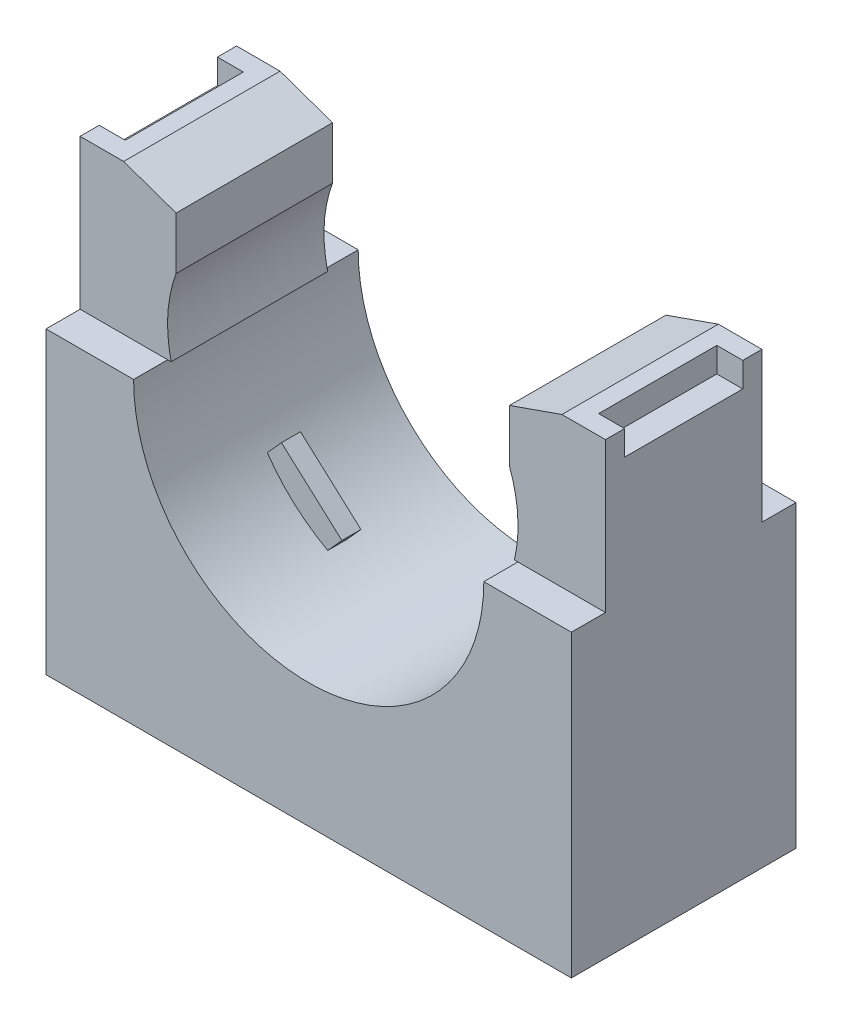
SolidWorks part; units mm, degrees
ref_plane "Front Plane" through (0, 0, 0) normal (0, 0, 1) x (1, 0, 0)
ref_plane "Top Plane" through (0, 0, 0) normal (0, 1, 0) x (1, 0, 0)
ref_plane "Right Plane" through (0, 0, 0) normal (1, 0, 0) x (0, 0, -1)
sketch "Sketch1" plane through (0, 0, 0) normal (0, 0, 1) x (1, 0, 0)
  line L0 (-17.526, -14.986) -> (17.526, 14.986) construction
  line L1 (-17.526, 14.986) -> (17.526, 14.986)
  line L2 (-17.526, 14.986) -> (-17.526, -14.986)
  line L3 (-17.526, -14.986) -> (17.526, -14.986)
  line L4 (17.526, 14.986) -> (17.526, -14.986)
  arc A0 (-11.4485, 2.6611) -> (11.4525, 2.6811) centre (0, 4.9953) ccw construction
  point P4 (0, 0)
  dimension "D3" = 19.9813
  dimension "D4" = 11.684
  dimension "B" = 35.052
  dimension "C" = 29.972
extrude "Extrude1" add sketch "Sketch1" along normal blind 14.986
sketch "Sketch2" plane through (0, 0, 14.986) normal (0, 0, 1) x (1, 0, 0)
  line L1 (-11.684, 4.9953) -> (-11.4503, 4.9953)
  line L2 (11.4503, 4.9953) -> (11.684, 4.9953)
  line L3 (11.1204, 10.2579) -> (11.1204, 13.7583)
  line L4 (11.1204, 13.7583) -> (14.6209, 14.986)
  line L5 (17.526, 14.986) -> (-17.526, 14.986) construction
  line L6 (0, 0) -> (0, 22.8281) construction
  line L7 (-11.1204, 13.7583) -> (-14.6209, 14.986)
  line L8 (-11.1204, 10.2579) -> (-11.1204, 13.7583)
  line L9 (14.6209, 14.986) -> (-14.6209, 14.986)
  line L10 (17.526, -14.986) -> (17.526, 14.986) construction
  arc A0 (-11.684, 4.9953) -> (11.684, 4.9953) centre (0, 4.9953) ccw
  arc A1 (11.1204, 10.2579) -> (11.4503, 4.9953) centre (2.5551, 7.0794) cw
  arc A2 (-11.1204, 10.2579) -> (-11.4503, 4.9953) centre (-2.5551, 7.0794) ccw
  arc A3 (-11.4485, 2.6611) -> (11.4525, 2.6811) centre (0, 4.9953) ccw construction
  dimension "D1" = 0.2337
  dimension "D3" = 9.1361
  dimension "D2" = 3.5004
  dimension "D4" = 3.5004
  dimension "D7" = 6.4056
  dimension "D8" = 5.2626
extrude "Cut-Extrude1" cut sketch "Sketch2" against normal through all
sketch "Sketch3" plane through (0, 0, 0) normal (1, 0, 0) x (0, 0, -1)
  line L1 (-14.986, 4.9953) -> (-12.7114, 4.9953)
  line L2 (-12.7114, 14.986) -> (-12.7114, 4.9953)
  line L3 (-14.986, 4.9953) -> (-14.986, 14.986)
  line L4 (-2.2746, 14.986) -> (-2.2746, 4.9953)
  line L5 (-7.493, 31.6865) -> (-7.493, 10.4775) construction
  line L6 (-14.986, 14.986) -> (0, 14.986) construction
  line L7 (-14.986, -14.986) -> (-14.986, 14.986) construction
  line L8 (-14.986, 14.986) -> (-12.7114, 14.986)
  line L9 (0, 4.9953) -> (0, 14.986)
  line L10 (0, 4.9953) -> (-2.2746, 4.9953)
  line L11 (-2.2746, 14.986) -> (0, 14.986)
  line L13 (0, -14.986) -> (0, 14.986) construction
  dimension "D2" = 2.2746
extrude "Cut-Extrude2" cut sketch "Sketch3" against normal through all and the other way through all
sketch "Sketch4" plane through (0, -14.986, 0) normal (0, -1, 0) x (1, 0, 0)
  line L12 (-17.526, 14.1922) -> (17.526, 14.1922)
  line L13 (-16.7322, 14.1922) -> (16.7323, 14.1922)
  line L14 (-16.7322, 0.7937) -> (-16.7322, 14.986)
  line L15 (16.7323, 0.7937) -> (-16.7322, 0.7937)
  line L16 (16.7323, 14.986) -> (16.7323, 0.7937)
  line L17 (-16.7322, 0.7937) -> (-16.7322, 14.1922)
  line L18 (16.7323, 0.7937) -> (-16.7322, 0.7937)
  line L19 (16.7323, 14.1922) -> (16.7323, 0.7937)
  dimension "D1" = 0.7937
  dimension "D2" = 0.7937
extrude "Cut-Extrude3" cut sketch "Sketch4" against normal blind 0.254
sketch "Sketch5" plane through (0, 14.986, 0) normal (0, 1, 0) x (1, 0, 0)
  line L0 (-17.526, -2.2746) -> (-14.6209, -2.2746) construction
  line L2 (-17.526, -3.5503) -> (-15.7946, -3.5503)
  line L3 (-17.526, -3.5503) -> (-17.526, -11.4357)
  line L4 (-17.526, -11.4357) -> (-15.7946, -11.4357)
  line L6 (-15.7946, -3.5503) -> (-15.7946, -11.4357)
  line L10 (17.526, -3.5503) -> (15.7946, -3.5503)
  line L11 (17.526, -3.5503) -> (17.526, -11.4357)
  line L12 (17.526, -11.4357) -> (15.7946, -11.4357)
  line L13 (15.7946, -3.5503) -> (15.7946, -11.4357)
  line L14 (17.526, -12.7114) -> (17.526, -2.2746) construction
  line L15 (-17.526, -12.7114) -> (-17.526, -2.2746) construction
  line L16 (14.6209, -7.493) -> (-14.6209, -7.493) construction
  line L17 (14.6209, -2.2746) -> (14.6209, -12.7114) construction
  line L18 (-14.6209, -2.2746) -> (-14.6209, -12.7114) construction
  dimension "D1" = 1.2757
  dimension "D2" = 1.1737
extrude "Cut-Extrude4" cut sketch "Sketch5" against normal blind 1.651
ref_plane "Plane1" through (0, 0, 7.493) normal (0, 0, -1) x (-1, 0, 0)
sketch "Sketch6" plane through (0, 0, 7.493) normal (0, 0, -1) x (-1, 0, 0)
  line L0 (0, 0) -> (0, -34.0604) construction
  line L1 (3.048, -14.732) -> (0, -14.732)
  line L2 (16.7322, -14.732) -> (-16.7323, -14.732) construction
  line L3 (0, -8.636) -> (5.969, -8.636)
  line L4 (5.969, -8.636) -> (5.969, -11.684)
  line L5 (5.969, -11.684) -> (3.048, -11.684)
  line L6 (3.048, -11.684) -> (3.048, -14.732)
  line L7 (0, -14.732) -> (0, -8.636)
  dimension "E" = 11.938
  dimension "D" = 6.096
  dimension "D3" = 3.048
  dimension "D4" = 6.096
revolve "Cut-Revolve1" cut sketch "Sketch6" angle 360 about L0
sketch "Sketch7" plane through (0, 0, 7.493) normal (0, 0, -1) x (-1, 0, 0)
  line L0 (0, 16.5622) -> (0, -24.4387) construction
  line L1 (0, 4.9953) -> (6.6588, -2.4) construction
  line L2 (4.6414, -4.2164) -> (8.6761, -0.5836)
  line L3 (8.6761, -0.5836) -> (9.6215, -1.6335)
  line L4 (4.6414, -4.2164) -> (5.5868, -5.2664)
  line L5 (-4.6414, -4.2164) -> (-5.5868, -5.2664)
  line L6 (-8.6761, -0.5836) -> (-9.6215, -1.6335)
  line L7 (-4.6414, -4.2164) -> (-8.6761, -0.5836)
  arc A0 (-11.4525, 2.6811) -> (11.4485, 2.6611) centre (0, 4.9953) ccw construction
  arc A3 (5.5868, -5.2664) -> (9.6215, -1.6335) centre (0, 4.9953) ccw
  arc A4 (-5.5868, -5.2664) -> (-9.6215, -1.6335) centre (0, 4.9953) cw
  point P9 (6.6588, -2.4)
  dimension "D1" = 42
  dimension "D2" = 5.4292
  dimension "D3" = 1.4129
extrude "Extrude2" add sketch "Sketch7" along normal mid plane 1.27
equation "\"D3@Sketch1\" = (\"C@Sketch1\"/3)*2"
equation "\"D4@Sketch1\" = \"B@Sketch1\"/3"
equation "\"D3@Sketch2\" = ((\"D4@Sketch1\"/4)*3)+0.0146875"
equation "\"D8@Sketch2\" = (\"D3@Sketch2\"/2)+0.02734375"
equation "\"D4@Sketch2\" = ((\"D8@Sketch2\"/4)*3)-0.009765625-0.0078125"
equation "\"D7@Sketch2\" = (\"D4@Sketch2\"*2)-0.0234375"
equation "\"D2@Sketch7\" = (\"D4@Sketch1\"/2)-0.01625"
equation "\"D3@Sketch7\" = \"D2@Sketch7\"/3-0.015625"
equation "\"D2@Sketch2\" = \"D4@Sketch2\""
equation "\"D1@Sketch2\" = \"D4@Sketch1\"/50"
equation "\"D4@Sketch6\" = \"D@Sketch6\""
equation "\"D3@Sketch6\" = \"D4@Sketch6\"/2"
